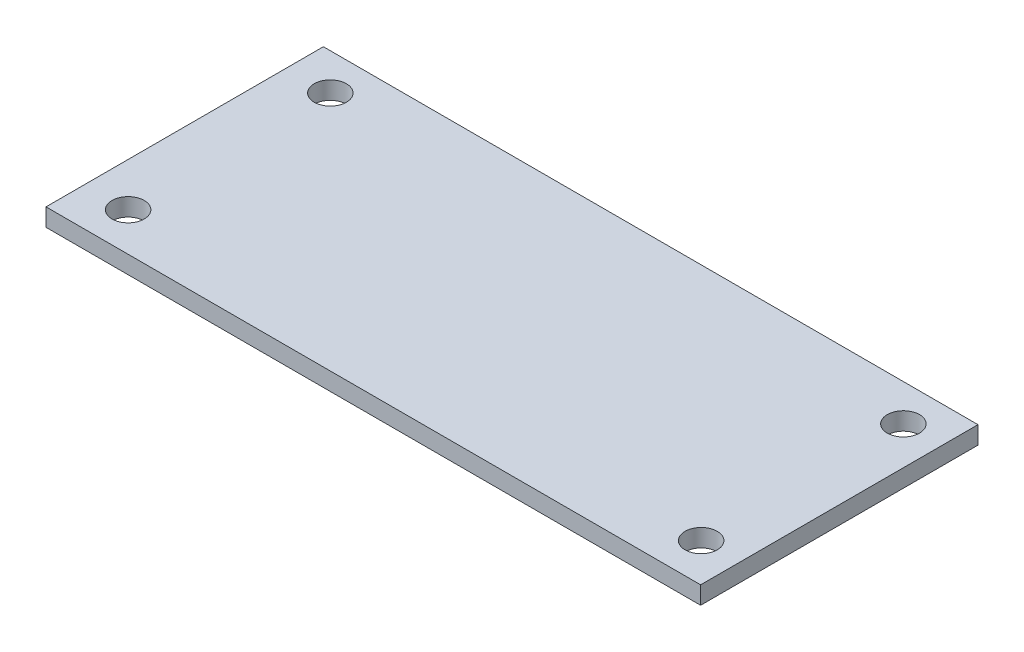
SolidWorks part; units mm, degrees
ref_plane "Front Plane" through (0, 0, 0) normal (0, 0, 1) x (1, 0, 0)
ref_plane "Top Plane" through (0, 0, 0) normal (0, 1, 0) x (1, 0, 0)
ref_plane "Right Plane" through (0, 0, 0) normal (1, 0, 0) x (0, 0, -1)
sketch "Sketch1" plane through (0, 0, 0) normal (0, 1, 0) x (1, 0, 0)
  line L1 (-29.972, 12.7) -> (29.972, 12.7)
  line L2 (-29.972, 12.7) -> (-29.972, -12.7)
  line L3 (-29.972, -12.7) -> (29.972, -12.7)
  line L4 (29.972, 12.7) -> (29.972, -12.7)
  line L5 (-29.972, 12.7) -> (29.972, -12.7) construction
  line L6 (-29.972, -12.7) -> (29.972, 12.7) construction
  point P0 (0, 0)
  dimension "D1" = 25.4
  dimension "D2" = 59.944
extrude "Boss-Extrude1" add sketch "Sketch1" along normal blind 1.6256
hole_wizard "#4 Clearance Hole1" positions "Sketch3" profile "Sketch2" hole size "#4" standard "ANSI Inch"
sketch "Sketch3" plane through (0, 0, 0) normal (0, -1, 0) x (-1, 0, 0)
  line L1 (25.9842, -9.1694) -> (-26.4922, -9.1694)
  line L2 (25.9842, -9.1694) -> (25.9842, 9.3472)
  line L3 (25.9842, 9.3472) -> (-26.4922, 9.3472)
  line L4 (-26.4922, -9.1694) -> (-26.4922, 9.3472)
  line L9 (29.972, 12.7) -> (29.972, -12.7) construction
  line L10 (-29.972, 12.7) -> (29.972, 12.7) construction
  point P0 (25.9842, -9.1694)
  point P2 (-26.4922, -9.1694)
  point P4 (-26.4922, 9.3472)
  point P6 (25.9842, 9.3472)
  dimension "D1" = 3.9878
  dimension "D2" = 3.3528
  dimension "D3" = 52.4764
  dimension "D4" = 18.5166
sketch "Sketch2" plane through (-25.9842, 0, 9.1694) normal (1, 0, 0) x (0, 0, -1)
  line L0 (0, 0) -> (0, 57.2732)
  line L1 (0, 57.2732) -> (1.4732, 56.388)
  line L2 (1.4732, 56.388) -> (1.4732, 0)
  line L5 (1.4732, 0) -> (0, 0)
  line L10 (0, 57.2732) -> (-1.4732, 56.388) construction
  line L11 (0, -6.35) -> (0, 107.95) construction
  dimension "Hole Dia." = 2.9464
  dimension "Hole Depth" = 56.388
  dimension "Drill Angle" = 118
